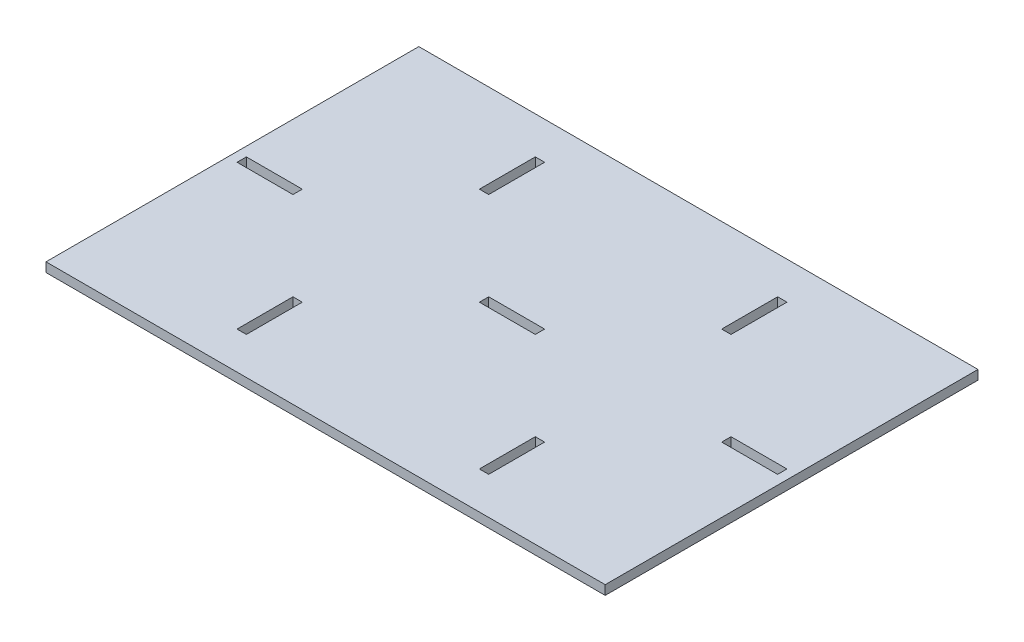
SolidWorks part; units mm, degrees
ref_plane "Front Plane" through (0, 0, 0) normal (0, 0, 1) x (1, 0, 0)
ref_plane "Top Plane" through (0, 0, 0) normal (0, 1, 0) x (1, 0, 0)
ref_plane "Right Plane" through (0, 0, 0) normal (1, 0, 0) x (0, 0, -1)
sketch "Sketch1" plane through (0, 0, 0) normal (0, 1, 0) x (1, 0, 0)
  line L1 (150, 100) -> (-150, 100)
  line L2 (150, 100) -> (150, -100)
  line L3 (150, -100) -> (-150, -100)
  line L4 (-150, 100) -> (-150, -100)
  line L5 (150, 100) -> (-150, -100) construction
  line L6 (150, -100) -> (-150, 100) construction
  point P0 (0, 0)
extrude "Boss-Extrude1" add sketch "Sketch1" along normal blind 5
sketch "Sketch2" plane through (0, 5, 0) normal (0, 1, 0) x (1, 0, 0)
  line L0 (0, 0) -> (-130, 0) construction
  line L2 (0, 0) -> (130, 0) construction
  line L5 (-115, 2.5) -> (-145, 2.5)
  line L6 (-115, 2.5) -> (-115, -2.5)
  line L7 (-115, -2.5) -> (-145, -2.5)
  line L8 (-145, 2.5) -> (-145, -2.5)
  line L9 (-115, 2.5) -> (-145, -2.5) construction
  line L10 (-115, -2.5) -> (-145, 2.5) construction
  line L11 (145, 2.5) -> (115, 2.5)
  line L12 (145, 2.5) -> (145, -2.5)
  line L13 (145, -2.5) -> (115, -2.5)
  line L14 (115, 2.5) -> (115, -2.5)
  line L15 (145, 2.5) -> (115, -2.5) construction
  line L16 (145, -2.5) -> (115, 2.5) construction
  line L17 (-62.5, 80) -> (-67.5, 80)
  line L18 (-62.5, 80) -> (-62.5, 50)
  line L19 (-62.5, 50) -> (-67.5, 50)
  line L20 (-67.5, 80) -> (-67.5, 50)
  line L21 (-62.5, 80) -> (-67.5, 50) construction
  line L22 (-62.5, 50) -> (-67.5, 80) construction
  line L23 (-62.5, -50) -> (-67.5, -50)
  line L24 (-62.5, -50) -> (-62.5, -80)
  line L25 (-62.5, -80) -> (-67.5, -80)
  line L26 (-67.5, -50) -> (-67.5, -80)
  line L27 (-62.5, -50) -> (-67.5, -80) construction
  line L28 (-62.5, -80) -> (-67.5, -50) construction
  line L29 (67.5, 80) -> (62.5, 80)
  line L30 (67.5, 80) -> (67.5, 50)
  line L31 (67.5, 50) -> (62.5, 50)
  line L32 (62.5, 80) -> (62.5, 50)
  line L33 (67.5, 80) -> (62.5, 50) construction
  line L34 (67.5, 50) -> (62.5, 80) construction
  line L35 (67.5, -80) -> (62.5, -80)
  line L36 (67.5, -80) -> (67.5, -50)
  line L37 (67.5, -50) -> (62.5, -50)
  line L38 (62.5, -80) -> (62.5, -50)
  line L39 (67.5, -80) -> (62.5, -50) construction
  line L40 (67.5, -50) -> (62.5, -80) construction
  line L41 (15, 2.5) -> (-15, 2.5)
  line L42 (15, 2.5) -> (15, -2.5)
  line L43 (15, -2.5) -> (-15, -2.5)
  line L44 (-15, 2.5) -> (-15, -2.5)
  line L45 (15, 2.5) -> (-15, -2.5) construction
  line L46 (15, -2.5) -> (-15, 2.5) construction
  point P17 (-65, 65)
  point P22 (-65, -65)
  point P27 (65, -65)
  point P28 (65, 65)
extrude "Cut-Extrude1" cut sketch "Sketch2" against normal blind 5
